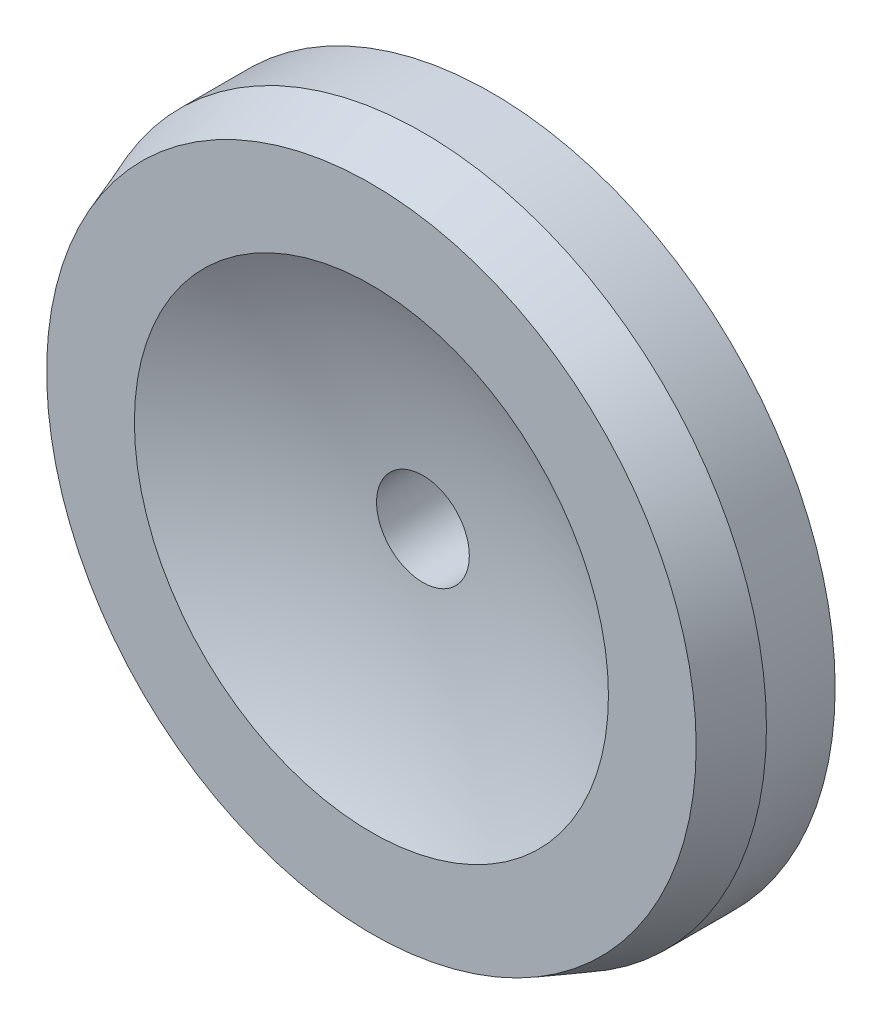
SolidWorks part; units mm, degrees
ref_plane "Alzado" through (0, 0, 0) normal (0, 0, 1) x (1, 0, 0)
ref_plane "Planta" through (0, 0, 0) normal (0, 1, 0) x (1, 0, 0)
ref_plane "Vista lateral" through (0, 0, 0) normal (1, 0, 0) x (0, 0, -1)
ref_plane "Plane1" through (0, -10.25, 0) normal (0, 1, 0) x (1, 0, 0)
sketch "Sketch1" plane through (0, -10.25, 0) normal (0, 1, 0) x (1, 0, 0)
  line L0 (1, -1.54) -> (1, -1.34)
  line L1 (1, -1.34) -> (0.135, -1.34)
  line L2 (0.135, -1.34) -> (0.135, -1.54)
  line L3 (0.69, -1.69) -> (0.9454, -1.69)
  line L4 (0.9454, -1.69) -> (1, -1.54)
  line L5 (0, -1.34) -> (0, -1.69) construction
  arc A0 (0.135, -1.54) -> (0.69, -1.69) centre (0, -3.1412) cw
  dimension "D1" = 1.6069
  dimension "D2" = 0.135
  dimension "D3" = 0.69
  dimension "D4" = 0.9454
  dimension "D5" = 1
  dimension "D6" = 0.2
revolve "Revolve1" add sketch "Sketch1" angle 360 about L5
